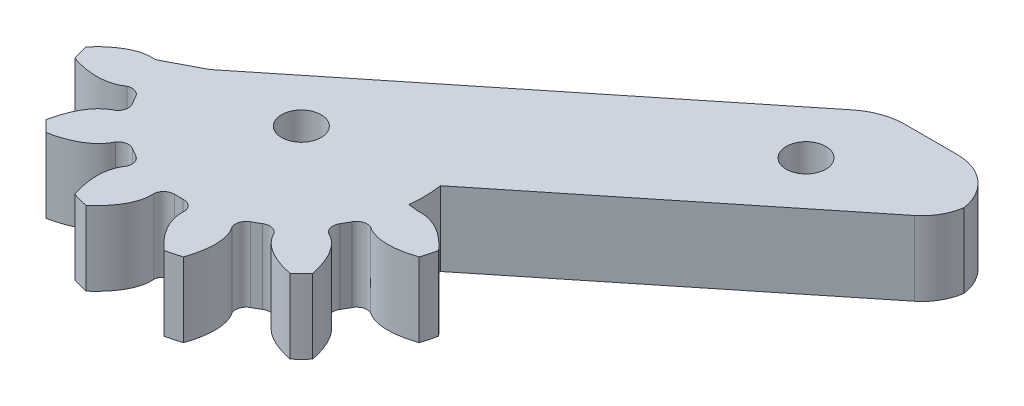
SolidWorks part; units mm, degrees
material "MDF"
ref_plane "Plano frontal" through (0, 0, 0) normal (0, 0, 1) x (1, 0, 0)
ref_plane "Plano superior" through (0, 0, 0) normal (0, 1, 0) x (1, 0, 0)
ref_plane "Plano direito" through (0, 0, 0) normal (1, 0, 0) x (0, 0, -1)
ref_plane "Plano1" through (0, -6, 0) normal (0, -1, 0) x (1, 0, 0)
sketch "Esboço1" plane through (0, -6, 0) normal (0, -1, 0) x (1, 0, 0)
  line L0 (24.2604, -24.5) -> (28.5, -24.5)
  line L1 (31.006, -18.507) -> (9.7886, -1.4529)
  line L2 (9.8296, 1.143) -> (10.6232, 1.2352)
  line L3 (-10.4667, 1.2071) -> (-7.6421, -0.2724)
  line L4 (-7.6421, -0.2724) -> (21.1279, -23.3971)
  line L5 (0, 0) -> (0, -24.5) construction
  line L6 (0, 0) -> (22.5984, -18.1641) construction
  line L7 (14.3216, -17.9264) -> (20.5865, -10.1321) construction
  arc A0 (28.5, -24.5) -> (32.4603, -21.0624) centre (28.5, -20.5) ccw
  arc A1 (32.4603, -21.0624) -> (31.006, -18.507) centre (28.5, -21.6247) ccw
  arc A2 (9.7886, -1.4529) -> (9.8296, 1.143) centre (0, 0) ccw
  arc A3 (10.6232, 1.2352) -> (10.6525, 1.2391) centre (10.7505, 0.3832) cw
  arc A4 (14.2396, 3.1474) -> (13.9056, 4.3941) centre (0, 0) ccw
  arc A5 (9.8449, 4.2532) -> (8.7409, 4.6395) centre (9.5018, 5.0434) cw
  arc A6 (8.7409, 4.6395) -> (8.3883, 5.2501) centre (0, 0) ccw
  arc A7 (8.3883, 5.2501) -> (8.6058, 6.3993) centre (9.1186, 5.7071) cw
  arc A8 (10.7582, 9.8456) -> (9.8456, 10.7582) centre (0, 0) ccw
  arc A9 (6.3993, 8.6058) -> (5.2501, 8.3883) centre (5.7071, 9.1186) cw
  arc A10 (5.2501, 8.3883) -> (4.6395, 8.7409) centre (0, 0) ccw
  arc A11 (4.6395, 8.7409) -> (4.2532, 9.8449) centre (5.0434, 9.5018) cw
  arc A12 (4.3941, 13.9056) -> (3.1474, 14.2396) centre (0, 0) ccw
  arc A13 (1.2391, 10.6525) -> (0.3525, 9.8896) centre (0.3832, 10.7505) cw
  arc A14 (0.3525, 9.8896) -> (-0.3525, 9.8896) centre (0, 0) ccw
  arc A15 (-0.3525, 9.8896) -> (-1.2391, 10.6525) centre (-0.3832, 10.7505) cw
  arc A16 (-3.1474, 14.2396) -> (-4.3941, 13.9056) centre (0, 0) ccw
  arc A17 (-4.2532, 9.8449) -> (-4.6395, 8.7409) centre (-5.0434, 9.5018) cw
  arc A18 (-4.6395, 8.7409) -> (-5.2501, 8.3883) centre (0, 0) ccw
  arc A19 (-5.2501, 8.3883) -> (-6.3993, 8.6058) centre (-5.7071, 9.1186) cw
  arc A20 (-9.8456, 10.7582) -> (-10.7582, 9.8456) centre (0, 0) ccw
  arc A21 (-8.6058, 6.3993) -> (-8.3883, 5.2501) centre (-9.1186, 5.7071) cw
  arc A22 (-8.3883, 5.2501) -> (-8.7409, 4.6395) centre (0, 0) ccw
  arc A23 (-8.7409, 4.6395) -> (-9.8449, 4.2532) centre (-9.5018, 5.0434) cw
  arc A24 (-13.9056, 4.3941) -> (-14.2396, 3.1474) centre (0, 0) ccw
  arc A25 (-10.6525, 1.2391) -> (-10.4658, 1.1963) centre (-10.7505, 0.3832) cw
  arc A26 (-10.4658, 1.1963) -> (-10.4667, 1.2071) centre (-25, 0) ccw
  arc A27 (21.1279, -23.3971) -> (24.2604, -24.5) centre (24.2604, -19.5) ccw
  circle A28 centre (0, 0) radius 1.6
  circle A29 centre (22.5984, -18.1641) radius 1.6
  ellipse E0 centre (12.658, 10.7674) end of major axis (10.2742, 1.3033) minor radius 4.8741 (10.6525, 1.2391) -> (14.2396, 3.1474) ccw
  ellipse E1 centre (16.3459, -2.9959) end of major axis (9.5494, 4.0084) minor radius 4.8741 (13.9056, 4.3941) -> (9.8449, 4.2532) ccw
  ellipse E2 centre (5.5784, 15.6539) end of major axis (8.2461, 6.2658) minor radius 4.8741 (8.6058, 6.3993) -> (10.7582, 9.8456) ccw
  ellipse E3 centre (15.6539, 5.5784) end of major axis (25.0419, 2.9108) minor radius 4.8741 (9.8456, 10.7582) -> (6.3993, 8.6058) ccw
  ellipse E4 centre (-2.9959, 16.3459) end of major axis (4.0084, 9.5494) minor radius 4.8741 (4.2532, 9.8449) -> (4.3941, 13.9056) ccw
  ellipse E5 centre (10.7674, 12.658) end of major axis (20.2316, 15.0418) minor radius 4.8741 (3.1474, 14.2396) -> (1.2391, 10.6525) ccw
  ellipse E6 centre (-10.7674, 12.658) end of major axis (-1.3033, 10.2742) minor radius 4.8741 (-1.2391, 10.6525) -> (-3.1474, 14.2396) ccw
  ellipse E7 centre (2.9959, 16.3459) end of major axis (10.0002, 23.1424) minor radius 4.8741 (-4.3941, 13.9056) -> (-4.2532, 9.8449) ccw
  ellipse E8 centre (-15.6539, 5.5784) end of major axis (-6.2658, 8.2461) minor radius 4.8741 (-6.3993, 8.6058) -> (-9.8456, 10.7582) ccw
  ellipse E9 centre (-5.5784, 15.6539) end of major axis (-2.9108, 25.0419) minor radius 4.8741 (-10.7582, 9.8456) -> (-8.6058, 6.3993) ccw
  ellipse E10 centre (-16.3459, -2.9959) end of major axis (-23.1424, -10.0002) minor radius 4.8741 (-9.8449, 4.2532) -> (-13.9056, 4.3941) ccw
  ellipse E11 centre (-12.658, 10.7674) end of major axis (-15.0418, 20.2316) minor radius 4.8741 (-14.2396, 3.1474) -> (-10.6525, 1.2391) ccw
  point P12 (12.658, 10.7674)
  point P13 (17.3844, 9.577)
  point P14 (10.2742, 1.3033)
  point P15 (10.6525, 1.2391)
  point P16 (14.2396, 3.1474)
  point P17 (12.6372, 1.7684)
  point P18 (12.6789, 19.7665)
  point P26 (16.3459, -2.9959)
  point P27 (19.8439, 0.3983)
  point P28 (9.5494, 4.0084)
  point P29 (13.9056, 4.3941)
  point P30 (9.8449, 4.2532)
  point P31 (11.8283, 4.7871)
  point P32 (20.8634, -10.7788)
  point P44 (5.5784, 15.6539)
  point P45 (10.2669, 16.9861)
  point P46 (8.2461, 6.2658)
  point P47 (8.6058, 6.3993)
  point P48 (10.7582, 9.8456)
  point P49 (10.0599, 7.8501)
  point P50 (1.097, 23.4577)
  point P58 (15.6539, 5.5784)
  point P59 (25.0419, 2.9108)
  point P60 (16.9861, 10.2669)
  point P61 (9.8456, 10.7582)
  point P62 (6.3993, 8.6058)
  point P63 (7.8501, 10.0599)
  point P64 (23.4577, 1.097)
  point P76 (-2.9959, 16.3459)
  point P77 (4.0084, 9.5494)
  point P78 (-6.3901, 12.8479)
  point P79 (4.2532, 9.8449)
  point P80 (4.3941, 13.9056)
  point P81 (4.7871, 11.8283)
  point P82 (-10.7788, 20.8634)
  point P90 (10.7674, 12.658)
  point P91 (20.2316, 15.0418)
  point P92 (9.577, 17.3844)
  point P93 (3.1474, 14.2396)
  point P94 (1.2391, 10.6525)
  point P95 (1.7684, 12.6372)
  point P96 (19.7665, 12.6789)
  point P108 (-10.7674, 12.658)
  point P109 (-1.3033, 10.2742)
  point P110 (-11.9579, 7.9316)
  point P111 (-1.2391, 10.6525)
  point P112 (-3.1474, 14.2396)
  point P113 (-1.7684, 12.6372)
  point P114 (-19.7665, 12.6789)
  point P122 (2.9959, 16.3459)
  point P123 (10.0002, 23.1424)
  point P124 (-0.3983, 19.8439)
  point P125 (-4.3941, 13.9056)
  point P126 (-4.2532, 9.8449)
  point P127 (-4.7871, 11.8283)
  point P128 (10.7788, 20.8634)
  point P140 (-15.6539, 5.5784)
  point P141 (-6.2658, 8.2461)
  point P142 (-14.3216, 0.89)
  point P143 (-6.3993, 8.6058)
  point P144 (-9.8456, 10.7582)
  point P145 (-7.8501, 10.0599)
  point P146 (-23.4577, 1.097)
  point P154 (-5.5784, 15.6539)
  point P155 (-0.89, 14.3216)
  point P156 (-2.9108, 25.0419)
  point P157 (-10.7582, 9.8456)
  point P158 (-8.6058, 6.3993)
  point P159 (-10.0599, 7.8501)
  point P160 (-1.097, 23.4577)
  point P172 (-16.3459, -2.9959)
  point P173 (-12.8479, -6.3901)
  point P174 (-23.1424, -10.0002)
  point P175 (-9.8449, 4.2532)
  point P176 (-13.9056, 4.3941)
  point P177 (-11.8283, 4.7871)
  point P178 (-20.8634, -10.7788)
  point P186 (-12.658, 10.7674)
  point P187 (-7.9316, 11.9579)
  point P188 (-15.0418, 20.2316)
  point P189 (-14.2396, 3.1474)
  point P190 (-10.6525, 1.2391)
  point P191 (-12.6372, 1.7684)
  point P192 (-12.6789, 19.7665)
  point P212 (17.4541, -14.0293)
  point P214 (26.3802, -24.5)
  dimension "D2" = 4
  dimension "D3" = 5
  dimension "D5" = 3.2
  dimension "D1" = 10
  dimension "D4" = 28.9935
  dimension "D6" = 51.208
  dimension "D7" = 6.3359
  dimension "D8" = 2.8982
  dimension "D9" = 9.8619
extrude "Ressalto-extrusão1" add sketch "Esboço1" against normal blind 6
